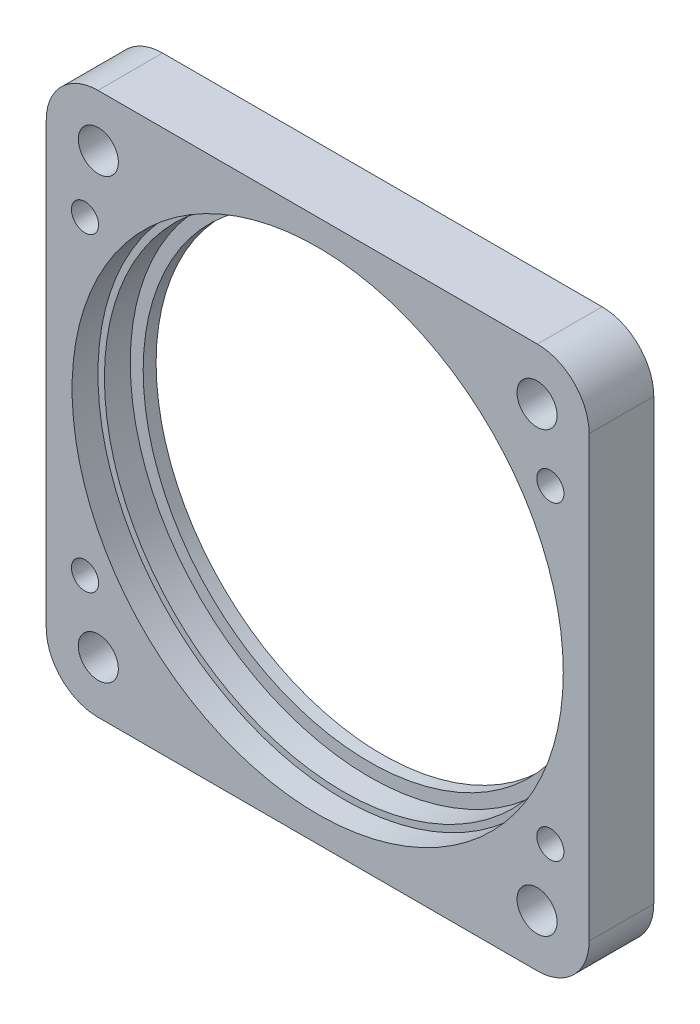
SolidWorks part; units mm, degrees
ref_plane "前视基准面" through (0, 0, 0) normal (0, 0, 1) x (1, 0, 0)
ref_plane "上视基准面" through (0, 0, 0) normal (0, 1, 0) x (1, 0, 0)
ref_plane "右视基准面" through (0, 0, 0) normal (1, 0, 0) x (0, 0, -1)
sketch "草图1" plane through (0, 0, 0) normal (0, 0, 1) x (1, 0, 0)
  line L1 (-21, 21) -> (21, 21)
  line L2 (-21, 21) -> (-21, -21)
  line L3 (-21, -21) -> (21, -21)
  line L4 (21, 21) -> (21, -21)
  line L5 (0, -21) -> (0, 21) construction
  line L6 (-21, 0) -> (21, 0) construction
  point P0 (0, 0)
  dimension "D1" = 42
  dimension "D2" = 42
extrude "凸台-拉伸1" add sketch "草图1" along normal blind 5
sketch "草图2" plane through (0, 0, 5) normal (0, 0, 1) x (1, 0, 0)
  circle A0 centre (0, 0) radius 17.5
  dimension "D1" = 35
extrude "切除-拉伸1" cut sketch "草图2" against normal through all
sketch "草图3" plane through (0, 0, 5) normal (0, 0, 1) x (1, 0, 0)
  circle A0 centre (0, 0) radius 18.5
  dimension "D1" = 37
extrude "切除-拉伸2" cut sketch "草图3" against normal offset from surface (4 mm away) 1 up to face at (17.5, 0, 0)
sketch "草图4" plane through (0, 0, 5) normal (0, 0, 1) x (1, 0, 0)
  circle A0 centre (0, 0) radius 19
  dimension "D1" = 38
extrude "切除-拉伸3" cut sketch "草图4" against normal offset from surface (2 mm away) 2 contours A0 up to face at (18.5, 0, 1)
fillet "圆角1" radius 4 4 edges at (-21, -21, 2.5) (21, -21, 2.5) (21, 21, 2.5) (-21, 21, 2.5)
sketch "草图5" plane through (0, 0, 5) normal (0, 0, 1) x (1, 0, 0)
  circle A0 centre (-16.9706, 16.9706) radius 1.55
  circle A3 centre (16.9706, 16.9706) radius 1.55
  circle A4 centre (16.9706, -16.9706) radius 1.55
  circle A5 centre (-16.9706, -16.9706) radius 1.55
  point P12 (0, 0)
  dimension "D1" = 3.1
  dimension "D2" = 24
  dimension "D4" = 4
sketch "草图6" plane through (0, 0, 5) normal (0, 0, 1) x (1, 0, 0)
  line L0 (-21, 17) -> (-21, -17) construction
  line L2 (-21, -9) -> (-21, -13)
  line L3 (-21, -13) -> (-17, -13)
  line L5 (-21, -9) -> (-17, -13)
  line L6 (-17, -21) -> (17, -21) construction
  line L7 (-9, 21) -> (-13, 17)
  line L8 (-13, 21) -> (-13, 17)
  line L9 (-9, 21) -> (-13, 21)
  line L10 (21, 9) -> (17, 13)
  line L11 (21, 13) -> (17, 13)
  line L12 (21, 9) -> (21, 13)
  line L13 (9, -21) -> (13, -17)
  line L14 (13, -21) -> (13, -17)
  line L15 (9, -21) -> (13, -21)
  point P19 (0, 0)
  dimension "D1" = 4
  dimension "D2" = 4
  dimension "D3" = 8
  dimension "D4" = 4
extrude "凸台-拉伸2" [suppressed] add sketch "草图6" along normal blind 3
pattern_circular "阵列(圆周)1" [suppressed] count 4 over 360
extrude "切除-拉伸4" cut sketch "草图5" against normal through all
sketch "草图7" plane through (0, 0, 0) normal (0, 0, -1) x (-1, 0, 0)
  line L0 (-21, -17) -> (-21, 17) construction
  line L1 (-17, 21) -> (17, 21) construction
  line L2 (-28.4314, 0) -> (27.643, 0) construction
  line L4 (0, 29.0062) -> (0, -29.8069) construction
  circle A0 centre (-18, 12) radius 1.05
  circle A4 centre (18, 12) radius 1.05
  circle A5 centre (18, -12) radius 1.05
  circle A6 centre (-18, -12) radius 1.05
  dimension "D1" = 2.1
  dimension "D2" = 3
  dimension "D3" = 9
extrude "切除-拉伸5" cut sketch "草图7" against normal through all
sketch "草图8" plane through (0, 0, 0) normal (0, 0, -1) x (-1, 0, 0)
  line L2 (-28.4314, 0) -> (27.643, 0) construction
  line L3 (-28.4314, 0) -> (27.643, 0) construction
  line L4 (0, 29.0062) -> (0, -29.8069) construction
  line L5 (0, 29.0062) -> (0, -29.8069) construction
  circle A0 centre (-18, 12) radius 2
  circle A1 centre (18, 12) radius 2
  circle A2 centre (18, -12) radius 2
  circle A3 centre (-18, -12) radius 2
  dimension "D1" = 4
extrude "切除-拉伸6" cut sketch "草图8" against normal blind 3
